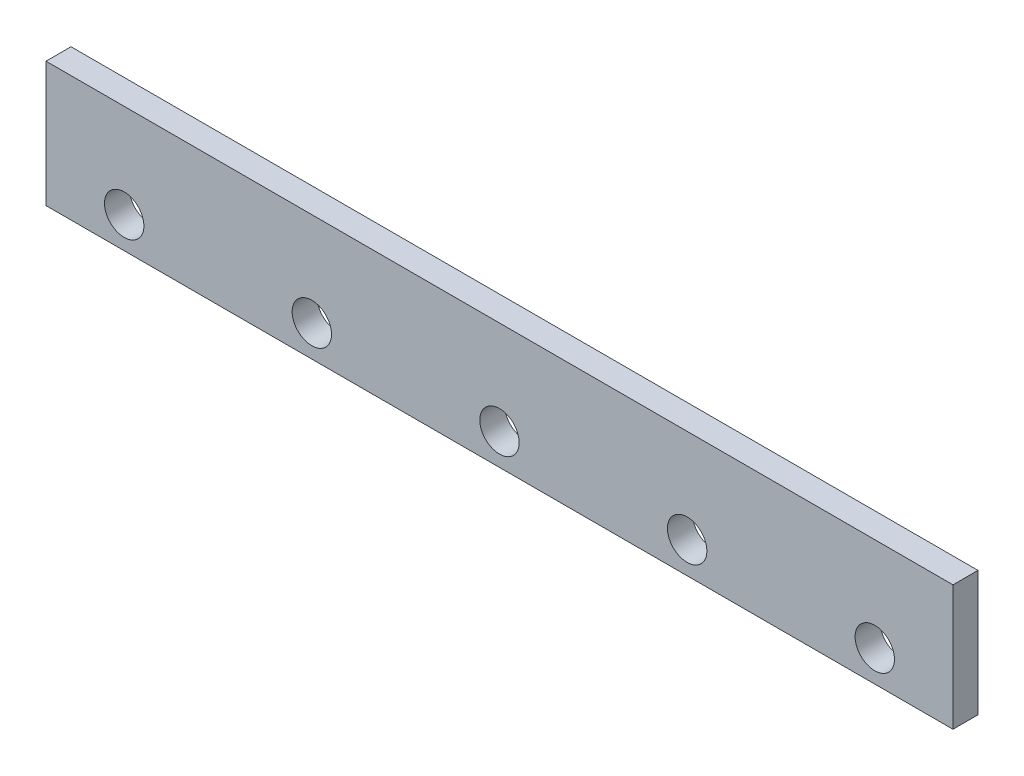
SolidWorks part; units mm, degrees
ref_plane "Front Plane" through (0, 0, 0) normal (0, 0, 1) x (1, 0, 0)
ref_plane "Top Plane" through (0, 0, 0) normal (0, 1, 0) x (1, 0, 0)
ref_plane "Right Plane" through (0, 0, 0) normal (1, 0, 0) x (0, 0, -1)
sketch "Sketch1" plane through (0, 0, 0) normal (0, 0, 1) x (1, 0, 0)
  line L0 (0, 0) -> (14732, 0)
  line L1 (14732, 0) -> (14732, 2032)
  line L2 (14732, 2032) -> (0, 2032)
  line L3 (0, 2032) -> (0, 0)
  circle A0 centre (1270, 508) radius 320.04
  circle A1 centre (4318, 508) radius 320.04
  circle A2 centre (7366, 508) radius 320.04
  circle A3 centre (10414, 508) radius 320.04
  circle A4 centre (13462, 508) radius 320.04
  dimension "D3" = 5
  dimension "D1" = 14732
  dimension "D2" = 2032
extrude "Boss-Extrude1" add sketch "Sketch1" along normal blind 406.4
